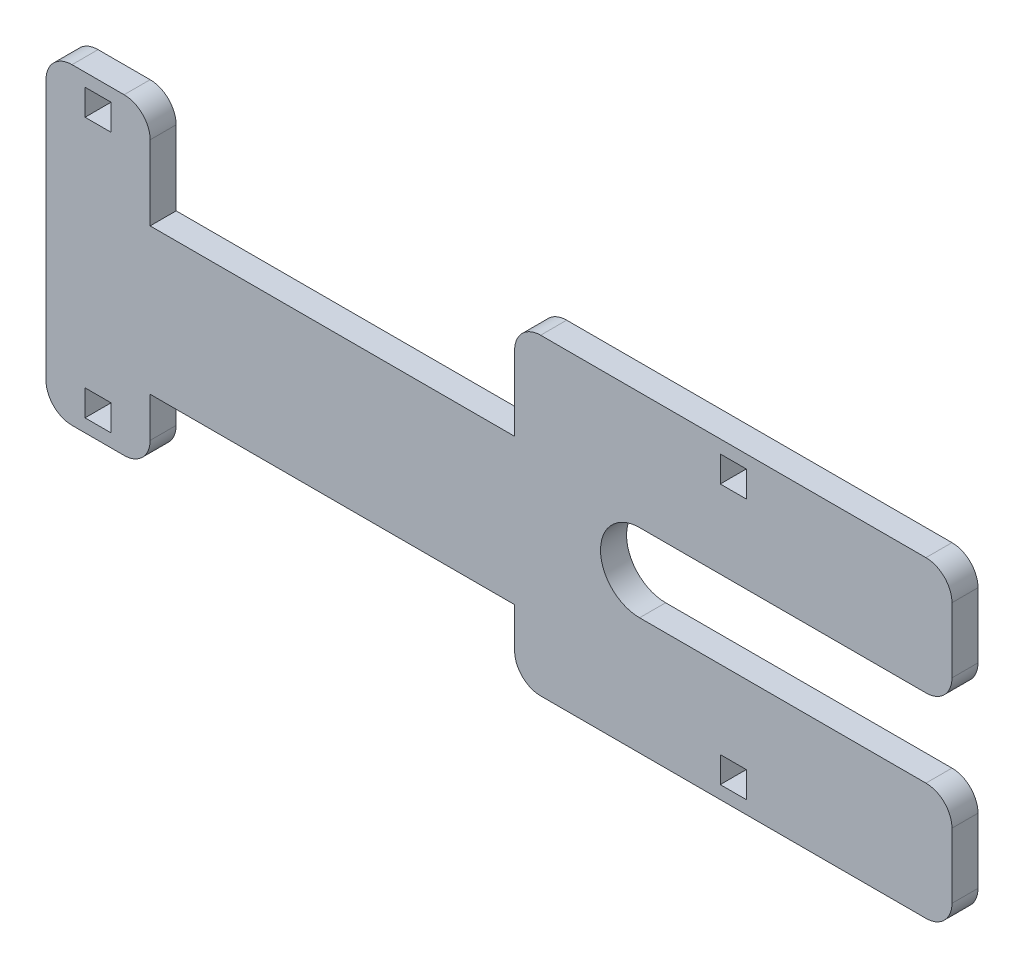
SolidWorks part; units mm, degrees
ref_plane "Front Plane" through (0, 0, 0) normal (0, 0, 1) x (1, 0, 0)
ref_plane "Top Plane" through (0, 0, 0) normal (0, 1, 0) x (1, 0, 0)
ref_plane "Right Plane" through (0, 0, 0) normal (1, 0, 0) x (0, 0, -1)
sketch "Sketch1" plane through (0, 0, 0) normal (0, 0, 1) x (1, 0, 0)
  line L32 (15.24, 15.7607) -> (50.165, 15.7607)
  line L33 (53.34, 18.9357) -> (53.34, 26.8732)
  line L34 (50.165, 30.0482) -> (3.175, 30.0482)
  line L35 (0, 26.8732) -> (0, 17.78)
  line L36 (0, 17.78) -> (-44.45, 17.78)
  line L37 (-44.45, 17.78) -> (-44.45, 26.8732)
  line L38 (-47.625, 30.0482) -> (-53.975, 30.0482)
  line L39 (-57.15, 26.8732) -> (-57.15, -4.8768)
  line L40 (-53.975, -8.0518) -> (-47.625, -8.0518)
  line L41 (-44.45, -4.8768) -> (-44.45, 0)
  line L42 (-44.45, 0) -> (0, 0)
  line L43 (0, 0) -> (0, -4.8768)
  line L44 (3.175, -8.0518) -> (50.165, -8.0518)
  line L45 (53.34, -4.8768) -> (53.34, 3.0607)
  line L46 (50.165, 6.2357) -> (15.24, 6.2357)
  arc A0 (50.165, 15.7607) -> (53.34, 18.9357) centre (50.165, 18.9357) ccw
  arc A1 (53.34, 3.0607) -> (50.165, 6.2357) centre (50.165, 3.0607) ccw
  arc A2 (15.24, 15.7607) -> (15.24, 6.2357) centre (15.24, 10.9982) ccw
  arc A20 (53.34, 26.8732) -> (50.165, 30.0482) centre (50.165, 26.8732) ccw
  arc A21 (3.175, 30.0482) -> (0, 26.8732) centre (3.175, 26.8732) ccw
  arc A22 (-44.45, 26.8732) -> (-47.625, 30.0482) centre (-47.625, 26.8732) ccw
  arc A23 (-53.975, 30.0482) -> (-57.15, 26.8732) centre (-53.975, 26.8732) ccw
  arc A24 (-57.15, -4.8768) -> (-53.975, -8.0518) centre (-53.975, -4.8768) ccw
  arc A25 (-47.625, -8.0518) -> (-44.45, -4.8768) centre (-47.625, -4.8768) ccw
  arc A26 (0, -4.8768) -> (3.175, -8.0518) centre (3.175, -4.8768) ccw
  arc A27 (50.165, -8.0518) -> (53.34, -4.8768) centre (50.165, -4.8768) ccw
  point P29 (-44.45, 22.3266)
  dimension "D1" = 17.78
  dimension "D2" = 53.34
  dimension "D3" = 3.175
  dimension "D4" = 38.1
  dimension "D5" = 44.45
  dimension "D6" = 12.7
  dimension "D7" = 3.175
  dimension "D8" = 38.1
  dimension "D9" = 9.525
  dimension "D10" = 12.2682
  dimension "D12" = 38.1
extrude "Boss-Extrude1" add sketch "Sketch1" along normal blind 3.175 contours L44 A27 L45 A1 L46 A2 L32 A0 L33 A20 L34 A21 L35 L36 L37 A22 L38 A23 L39 A24 L40 A25 L41 L42 L43 A26
sketch "Sketch2" plane through (0, 0, 3.175) normal (0, 0, 1) x (1, 0, 0)
  line L0 (-47.625, 30.0482) -> (-53.975, 30.0482) construction
  line L1 (25.0825, -6.4643) -> (28.2575, -6.4643)
  line L2 (25.0825, -6.4643) -> (25.0825, -3.2893)
  line L3 (25.0825, -3.2893) -> (28.2575, -3.2893)
  line L4 (28.2575, -6.4643) -> (28.2575, -3.2893)
  line L5 (-52.3875, 28.4607) -> (-49.2125, 28.4607)
  line L6 (-52.3875, 28.4607) -> (-52.3875, 25.2857)
  line L7 (-52.3875, 25.2857) -> (-49.2125, 25.2857)
  line L8 (-49.2125, 28.4607) -> (-49.2125, 25.2857)
  line L9 (3.175, -8.0518) -> (50.165, -8.0518) construction
  line L10 (-57.15, 10.9982) -> (48.5001, 10.9982) construction
  line L12 (-57.15, 26.8732) -> (-57.15, -4.8768) construction
  line L13 (25.0825, 28.4607) -> (28.2575, 28.4607)
  line L14 (25.0825, 28.4607) -> (25.0825, 25.2857)
  line L15 (28.2575, 28.4607) -> (28.2575, 25.2857)
  line L16 (25.0825, 25.2857) -> (28.2575, 25.2857)
  line L17 (-52.3875, -6.4643) -> (-49.2125, -6.4643)
  line L18 (-52.3875, -6.4643) -> (-52.3875, -3.2893)
  line L19 (-49.2125, -6.4643) -> (-49.2125, -3.2893)
  line L20 (-52.3875, -3.2893) -> (-49.2125, -3.2893)
  point P10 (-50.8, 30.0482)
  point P11 (-49.2125, 26.8732)
  point P12 (-50.8, 28.4607)
  point P15 (28.2575, -4.8768)
  point P16 (26.67, -6.4643)
  point P17 (26.67, -8.0518)
  point P21 (-57.15, 10.9982)
  dimension "D1" = 1.5875
  dimension "D2" = 3.175
  dimension "D3" = 3.175
  dimension "D4" = 1.5875
  dimension "D5" = 3.175
  dimension "D6" = 3.175
extrude "Cut-Extrude1" cut sketch "Sketch2" against normal through all both and the other way through all
